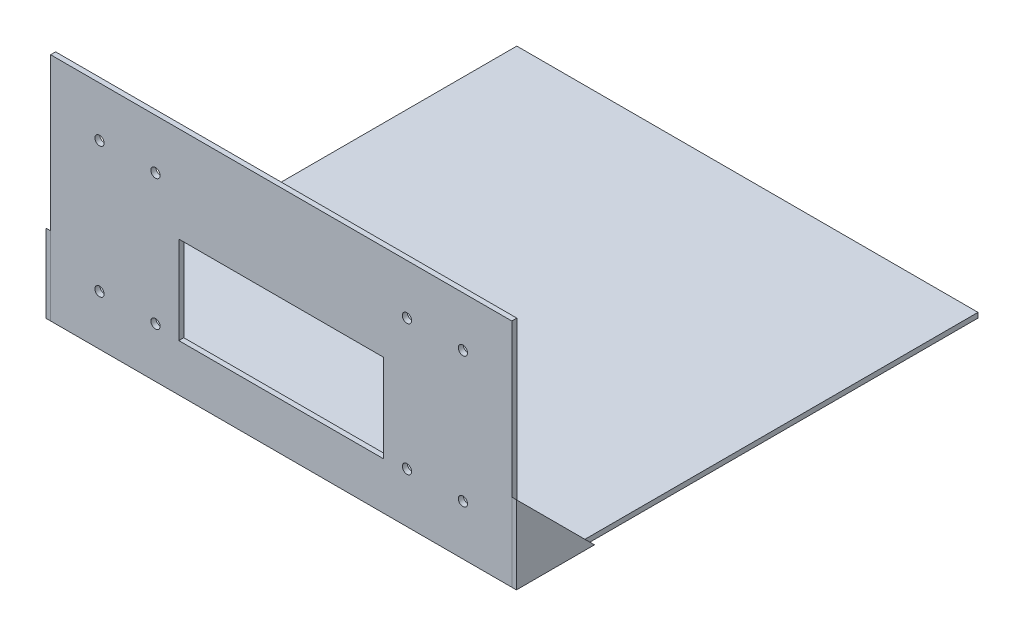
SolidWorks part; units mm, degrees
ref_plane "Front" through (0, 0, 0) normal (0, 0, 1) x (1, 0, 0)
ref_plane "Top" through (0, 0, 0) normal (0, 1, 0) x (1, 0, 0)
ref_plane "Right" through (0, 0, 0) normal (1, 0, 0) x (0, 0, -1)
sketch "Sketch1" plane through (0, 0, 0) normal (0, 1, 0) x (1, 0, 0)
  line L1 (150, 150) -> (-150, 150)
  line L2 (150, 150) -> (150, -150)
  line L3 (150, -150) -> (-150, -150)
  line L4 (-150, 150) -> (-150, -150)
  line L5 (150, 150) -> (-150, -150) construction
  line L6 (150, -150) -> (-150, 150) construction
  point P0 (0, 0)
  dimension "D1" = 300
  dimension "D2" = 300
extrude "Boss-Extrude1" add sketch "Sketch1" along normal blind 3.25 contours L1 L4 L3 L2
ref_plane "Plane1" through (0, 0, 150) normal (0, 0, 1) x (1, 0, 0)
sketch "Sketch2" plane through (0, 0, 150) normal (0, 0, 1) x (1, 0, 0)
  line L1 (150, 0) -> (-150, 0)
  line L2 (150, 0) -> (150, 150)
  line L3 (150, 150) -> (-150, 150)
  line L4 (-150, 0) -> (-150, 150)
  dimension "D1" = 150
extrude "Boss-Extrude2" add sketch "Sketch2" along normal blind 3.25 separate body
sketch "Sketch3" plane through (0, 0, 153.25) normal (0, 0, 1) x (1, 0, 0)
  line L1 (66.6163, 30.6506) -> (-66.6163, 30.6506)
  line L2 (66.6163, 30.6506) -> (66.6163, 87.8494)
  line L3 (66.6163, 87.8494) -> (-66.6163, 87.8494)
  line L4 (-66.6163, 30.6506) -> (-66.6163, 87.8494)
  line L5 (66.6163, 30.6506) -> (-66.6163, 87.8494) construction
  line L6 (66.6163, 87.8494) -> (-66.6163, 30.6506) construction
  point P0 (0, 59.25)
extrude "Cut-Extrude1" cut sketch "Sketch3" against normal blind 3.25
sketch "Sketch4" plane through (0, 0, 132.5) normal (0, 0, 1) x (1, 0, 0)
  circle A0 centre (81.7966, 117.5675) radius 3 construction
  circle A1 centre (118.2034, 117.5675) radius 3 construction
  circle A2 centre (118.2034, 32.5675) radius 3 construction
  circle A3 centre (81.7966, 32.5675) radius 3 construction
  circle A4 centre (-81.7966, 32.5675) radius 3 construction
  circle A5 centre (-118.2034, 32.5675) radius 3 construction
  circle A6 centre (-118.2034, 117.5675) radius 3 construction
  circle A7 centre (-81.7966, 117.5675) radius 3 construction
  circle A8 centre (81.7966, 117.5675) radius 3
  circle A9 centre (118.2034, 117.5675) radius 3
  circle A10 centre (118.2034, 32.5675) radius 3
  circle A11 centre (81.7966, 32.5675) radius 3
  circle A12 centre (-81.7966, 32.5675) radius 3
  circle A13 centre (-118.2034, 32.5675) radius 3
  circle A14 centre (-118.2034, 117.5675) radius 3
  circle A15 centre (-81.7966, 117.5675) radius 3
extrude "Cut-Extrude2" cut sketch "Sketch4" along normal through all
ref_plane "Plane2" through (-150, 0, 0) normal (-1, 0, 0) x (0, 0, 1)
ref_plane "Plane3" through (150, 0, 0) normal (1, 0, 0) x (0, 0, -1)
sketch "Sketch5" plane through (150, 0, 0) normal (1, 0, 0) x (0, 0, -1)
  line L0 (-153.25, 0) -> (-153.25, 50.8)
  line L1 (-153.25, 0) -> (-153.25, 150) construction
  line L2 (-153.25, 50.8) -> (-102.45, 0)
  line L3 (150, 0) -> (-150, 0) construction
  line L4 (-102.45, 0) -> (-153.25, 0)
  dimension "D1" = 50.8
extrude "Boss-Extrude3" add sketch "Sketch5" along normal blind 3 separate body contours L2 L4 L0
mirror "Mirror1" about plane through (0, 0, 0) normal (1, 0, 0) of bodies 105
